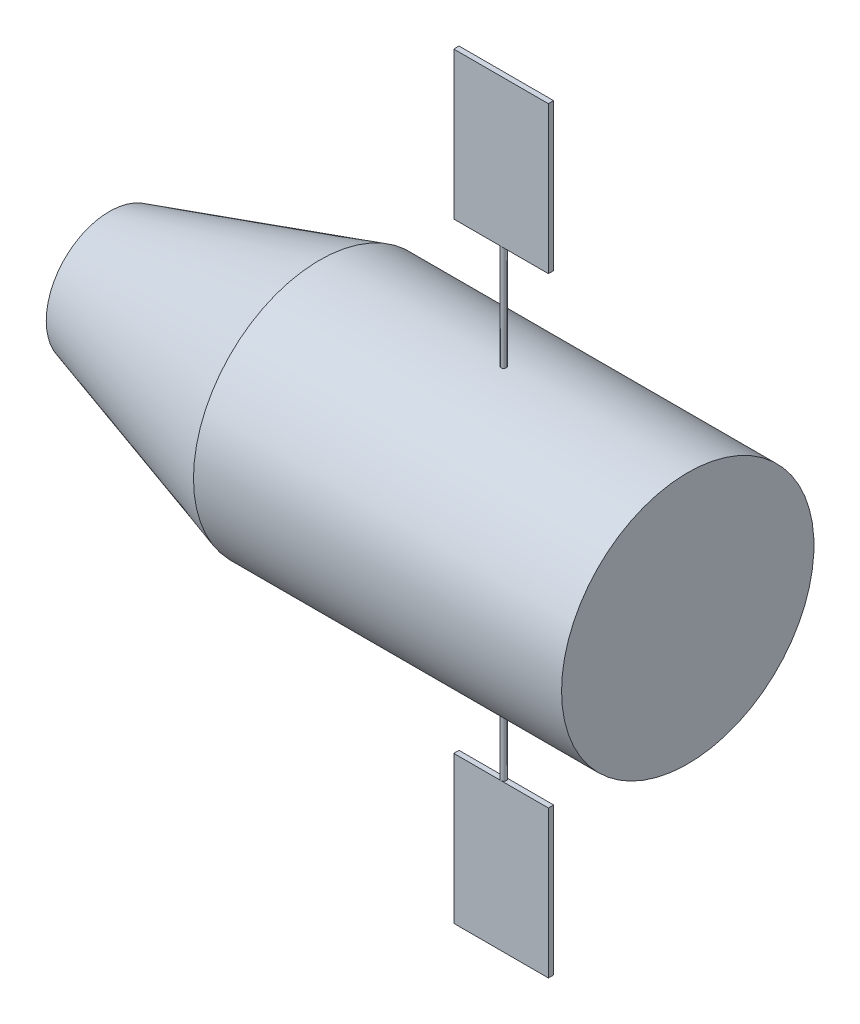
SolidWorks part; units mm, degrees
ref_plane "Front" through (0, 0, 0) normal (0, 0, 1) x (1, 0, 0)
ref_plane "Top" through (0, 0, 0) normal (0, 1, 0) x (1, 0, 0)
ref_plane "Right" through (0, 0, 0) normal (1, 0, 0) x (0, 0, -1)
sketch "Sketch1" plane through (0, 0, 0) normal (0, 0, 1) x (1, 0, 0)
  line L0 (0, 0) -> (110, 0)
  line L1 (110, 0) -> (110, 24)
  line L2 (110, 24) -> (40, 24)
  line L3 (40, 24) -> (0, 12)
  line L4 (0, 12) -> (0, 0)
  dimension "D1" = 24
  dimension "D2" = 110
  dimension "D3" = 12
  dimension "D4" = 70
revolve "Revolve1" add sketch "Sketch1" angle 360 about L0
sketch "Sketch2" plane through (0, 0, 0) normal (0, 1, 0) x (1, 0, 0)
  circle A0 centre (75, 0) radius 0.5
extrude "Extrude1" add sketch "Sketch2" along normal mid plane 88
sketch "Sketch3" plane through (0, 0, 0) normal (0, 0, 1) x (1, 0, 0)
  line L2 (66, 44) -> (84, 44)
  line L3 (66, 72) -> (84, 72)
  line L4 (66, 44) -> (66, 72)
  line L5 (84, 44) -> (84, 72)
  line L7 (75, 72) -> (90.1256, 72) construction
  line L8 (75, 44) -> (90.1256, 44) construction
  line L9 (66, -44) -> (66, -72)
  line L10 (84, -44) -> (84, -72)
  line L11 (66, -44) -> (84, -44)
  line L12 (66, -72) -> (84, -72)
extrude "Extrude2" add sketch "Sketch3" along normal mid plane 1 separate body
